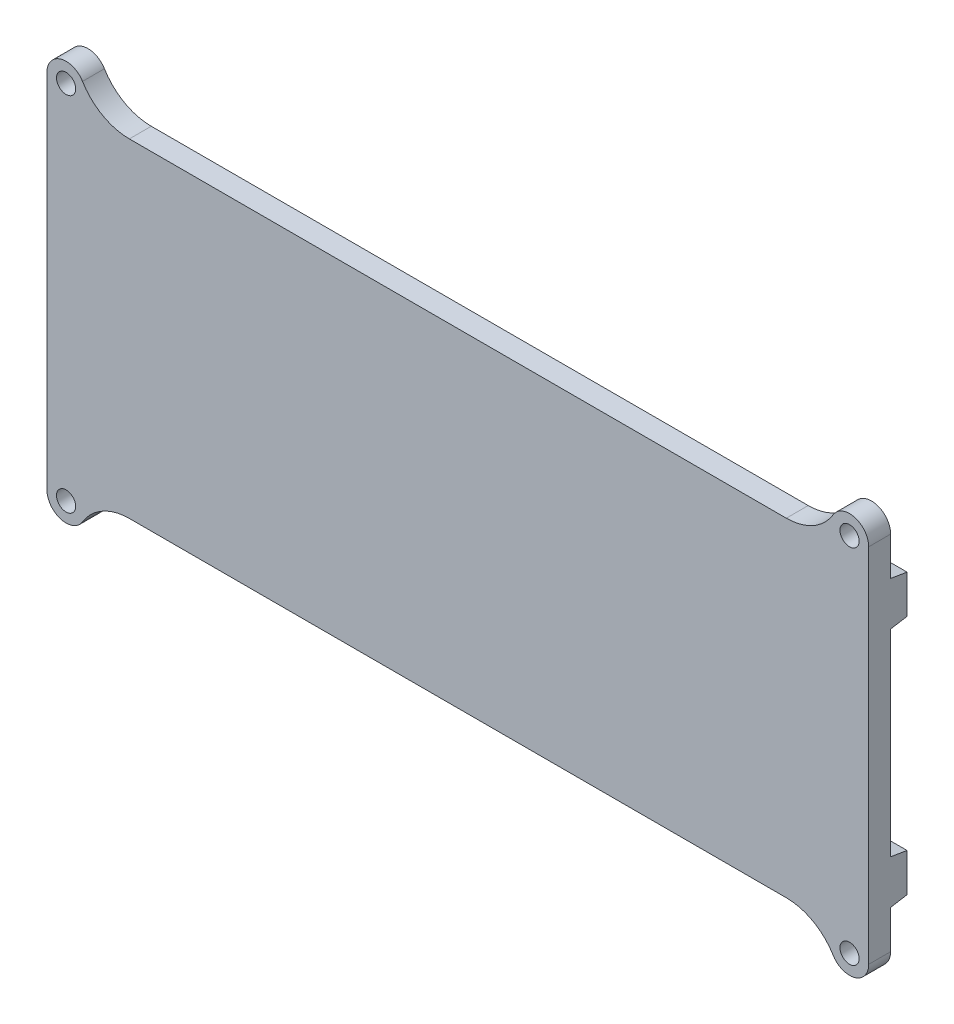
SolidWorks part; units mm, degrees
ref_plane "Piano frontale" through (0, 0, 0) normal (0, 0, 1) x (1, 0, 0)
ref_plane "Piano superiore" through (0, 0, 0) normal (0, 1, 0) x (1, 0, 0)
ref_plane "Piano destro" through (0, 0, 0) normal (1, 0, 0) x (0, 0, -1)
sketch "Schizzo1" plane through (0, 0, 0) normal (0, 0, 1) x (1, 0, 0)
  line L5 (75, -30) -> (-75, -30)
  line L6 (75, -30) -> (75, 30)
  line L11 (75, 30) -> (-75, 30)
  line L20 (-75, -30) -> (-75, 30)
  line L21 (75, -30) -> (-75, 30) construction
  line L22 (75, 30) -> (-75, -30) construction
  point P0 (0, 0)
  dimension "D1" = 60
  dimension "D2" = 150
extrude "Estrusione-Estrusione1" add sketch "Schizzo1" along normal blind 4 contours L20 L11 L6 L5
ref_plane "Piano2" through (0, -30, 0) normal (0, -1, 0) x (-1, 0, 0)
ref_plane "Piano3" through (0, 0, 2) normal (0, 0, 1) x (1, 0, 0)
sketch "Schizzo5" plane through (0, 0, 0) normal (0, 0, -1) x (-1, 0, 0)
  line L1 (-75, 30) -> (-68, 30)
  line L2 (-75, 30) -> (-75, 33)
  line L4 (-68, 30) -> (-68, 33)
  arc A0 (-75, 33) -> (-68, 33) centre (-71.5, 33) cw
  circle A1 centre (-71.5, 33) radius 1.75
  dimension "D1" = 3
  dimension "D2" = 7
extrude "Estrusione-Estrusione3" add sketch "Schizzo5" against normal blind 4
mirror "Specchia5" about plane through (0, 0, 0) normal (1, 0, 0) of "Estrusione-Estrusione3"
mirror "Specchia6" about plane through (0, 0, 0) normal (0, 1, 0) of "Specchia5", "Estrusione-Estrusione3"
fillet "Raccordo2" radius 10 4 edges at (68, -30, 2) (-68, -30, 2) (68, 30, 2) (-68, 30, 2)
sketch "Schizzo6" plane through (75, 0, 0) normal (1, 0, 0) x (0, 0, -1)
  line L0 (0, -26) -> (3, -25.5)
  line L2 (3, -25.5) -> (3, -18.5)
  line L3 (3, -18.5) -> (0, -18)
  line L4 (0, -18) -> (0, -26)
  line L5 (0, -33) -> (0, 33) construction
  line L6 (-2.2, -30) -> (2.2, -30) construction
  dimension "D1" = 7
  dimension "D2" = 8
  dimension "D3" = 3
  dimension "D4" = 4
extrude "Estrusione-Estrusione4" add sketch "Schizzo6" against normal blind 4
mirror "Specchia7" about plane through (0, 0, 0) normal (1, 0, 0) of "Estrusione-Estrusione4"
mirror "Specchia8" about plane through (0, 0, 0) normal (0, 1, 0) of "Specchia7", "Estrusione-Estrusione4"
sketch "Schizzo7" plane through (0, 0, 4) normal (0, 0, 1) x (1, 0, 0)
  line L0 (78.5, 26.5) -> (75, 23)
  line L2 (78.5, 26.5) -> (78.5, 33.5)
  line L3 (78.5, 33.5) -> (71.5, 33.5)
  line L5 (78.5, 26.5) -> (71.5, 33.5) construction
  line L6 (78.5, 33.5) -> (71.5, 26.5) construction
  line L7 (75, -33) -> (75, 33) construction
  line L8 (75, 23) -> (75, 30)
  line L9 (75, 30) -> (68, 30)
  line L10 (59.9566, 30) -> (-59.9566, 30) construction
  line L11 (68, 30) -> (71.5, 33.5)
  point P0 (75, 30)
  dimension "D1" = 7
  dimension "D2" = 7
  dimension "D3" = 7
extrude "Estrusione-Estrusione5" [suppressed] add sketch "Schizzo7" against normal blind 10
mirror "Specchia11" [suppressed] about plane through (0, 0, 0) normal (1, 0, 0)
mirror "Specchia12" [suppressed] about plane through (0, 0, 0) normal (0, 1, 0)
sketch "Schizzo8" plane through (0, 0, 0) normal (0, 1, 0) x (1, 0, 0)
  line L0 (75.0971, 0.4855) -> (75.2039, 1.0194)
  line L1 (75.2039, 2.9806) -> (75.0971, 3.5145)
  line L2 (75, 4.4951) -> (75, 10.0175)
  line L3 (75.3241, 11.7883) -> (76.0324, 13.6587)
  line L4 (77, 13.4816) -> (77, 4.4951)
  line L5 (77, -4) -> (75, -4)
  line L6 (75, -4) -> (75, -0.4951)
  line L8 (76.9029, 3.5145) -> (76.7302, 2.6509)
  line L9 (76.6442, 1.3377) -> (77, -4)
  arc A0 (75, 10.0175) -> (75.3241, 11.7883) centre (80, 10.0175) cw
  arc A1 (75.0971, 3.5145) -> (75, 4.4951) centre (80, 4.4951) cw
  arc A2 (75.0971, 0.4855) -> (75, -0.4951) centre (80, -0.4951) ccw
  arc A3 (76.9029, 3.5145) -> (77, 4.4951) centre (72, 4.4951) ccw
  arc A4 (76.7302, 2.6509) -> (76.6442, 1.3377) centre (81.6331, 1.6703) ccw
  arc A5 (75.2039, 1.0194) -> (75.2039, 2.9806) centre (70.301, 2) ccw
  arc A6 (76.0324, 13.6587) -> (77, 13.4816) centre (76.5, 13.4816) cw
  point P13 (75, 4)
  point P16 (75, 0)
  point P24 (76.6, 2)
  point P28 (75.4, 2)
  dimension "D5" = 5
  dimension "D7" = 0.5
  dimension "D1" = 2
  dimension "D2" = 0.4
  dimension "D3" = 4
  dimension "D4" = 0.4
  dimension "D6" = 2
extrude "Estrusione-Estrusione6" [suppressed] add sketch "Schizzo8" along normal mid plane 20
sketch "Schizzo9" [suppressed] plane through (0, 0, 0) normal (0, 1, 0) x (1, 0, 0)
  line L0 (75, 8) -> (75.35, 8)
  line L1 (75.35, 8) -> (75, 6)
  line L2 (75, 6) -> (75, 8)
  line L3 (75, 10.0175) -> (75, 4.4951) construction
  line L4 (-36.85, 0) -> (36.85, 0) construction
  dimension "D1" = 0.35
  dimension "D2" = 2
  dimension "D3" = 8
extrude "Taglio-Estrusione2" [suppressed] cut sketch "Schizzo9" against normal mid plane 10
mirror "Specchia13" [suppressed] about plane through (0, 0, 0) normal (1, 0, 0)
